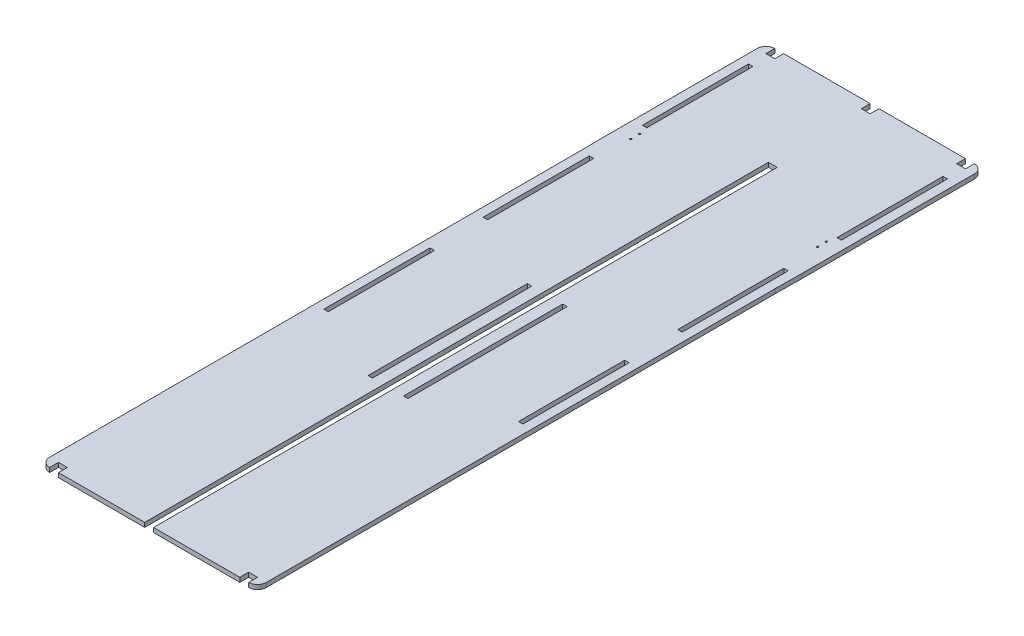
SolidWorks part; units mm, degrees
ref_plane "Front" through (0, 0, 0) normal (0, 0, 1) x (1, 0, 0)
ref_plane "Top" through (0, 0, 0) normal (0, 1, 0) x (1, 0, 0)
ref_plane "Right" through (0, 0, 0) normal (1, 0, 0) x (0, 0, -1)
sketch "Sketch2" plane through (0, 0, 0) normal (0, 1, 0) x (1, 0, 0)
  line L0 (122.5, 590) -> (122.5, -185) construction
  line L2 (0, 0) -> (0, 375)
  line L3 (0, 590) -> (245, 590)
  line L4 (245, -10) -> (245, 355)
  line L5 (10, 590) -> (10, -230) construction
  line L7 (117.5, -230) -> (117.5, 475)
  line L8 (117.5, 475) -> (127.5, 475)
  line L9 (127.5, -230) -> (127.5, 475)
  line L10 (117.5, -230) -> (127.5, 475) construction
  line L11 (117.5, 475) -> (127.5, -230) construction
  line L12 (10, -230) -> (15, -230)
  line L13 (15, -230) -> (15, 590) construction
  line L14 (235, 590) -> (235, -230) construction
  line L15 (235, -230) -> (230, -230)
  line L16 (230, -230) -> (230, 590) construction
  line L18 (0, 0) -> (0, -230)
  line L19 (245, -10) -> (245, -230)
  line L20 (0, -230) -> (117.5, -230)
  line L21 (127.5, -230) -> (245, -230)
  line L22 (-0.3, 405) -> (0, 375)
  line L23 (-0.3, 405) -> (-0.3, 590)
  line L24 (-0.3, 590) -> (0, 590)
  line L25 (10, 560) -> (15, 560)
  line L26 (245.3, 385) -> (245, 355)
  line L27 (245.3, 385) -> (245.3, 590)
  line L28 (245.3, 590) -> (245, 590)
  line L29 (10, 560) -> (10, 440)
  line L30 (10, 440) -> (15, 440)
  line L31 (15, 560) -> (15, 440)
  line L32 (15, 380) -> (10, 380)
  line L33 (15, 380) -> (15, 260)
  line L34 (15, 260) -> (10, 260)
  line L35 (10, 380) -> (10, 260)
  line L36 (10, 200) -> (15, 200)
  line L37 (10, 200) -> (10, 80)
  line L38 (10, 80) -> (15, 80)
  line L39 (15, 200) -> (15, 80)
  line L40 (230, 560) -> (235, 560)
  line L41 (230, 560) -> (230, 440)
  line L42 (230, 440) -> (235, 440)
  line L43 (235, 560) -> (235, 440)
  line L44 (230, 380) -> (235, 380)
  line L45 (230, 380) -> (230, 260)
  line L46 (230, 260) -> (235, 260)
  line L47 (235, 380) -> (235, 260)
  line L48 (230, 200) -> (235, 200)
  line L49 (230, 200) -> (230, 80)
  line L50 (230, 80) -> (235, 80)
  line L51 (235, 200) -> (235, 80)
  point P7 (122.5, 122.5)
  dimension "D1" = 245
  dimension "D2" = 820
  dimension "D3" = 115
  dimension "D4" = 10
  dimension "D5" = 590
  dimension "D6" = 10
  dimension "D7" = 5
  dimension "D8" = 10
  dimension "D9" = 5
  dimension "D10" = 30
  dimension "D11" = 120
  dimension "D12" = 60
  dimension "D13" = 0.3
  dimension "D14" = 30
  dimension "D15" = 30
  dimension "D16" = 120
  dimension "D17" = 60
  dimension "D18" = 120
  dimension "D19" = 120
  dimension "D20" = 60
  dimension "D21" = 120
  dimension "D22" = 60
  dimension "D23" = 120
extrude "Boss-Extrude1" add sketch "Sketch2" along normal blind 5
sketch "Sketch3" plane through (0, 5, 0) normal (0, 1, 0) x (1, 0, 0)
  line L0 (17, 510.3998) -> (17, 370) construction
  line L1 (0, -230) -> (0, 375) construction
  line L2 (-0.3, 590) -> (245.3, 590) construction
  line L3 (117.5, 475) -> (127.5, 475) construction
  line L4 (105, 220) -> (100, 220)
  line L5 (105, 220) -> (105, 40)
  line L6 (105, 40) -> (100, 40)
  line L7 (100, 220) -> (100, 40)
  line L8 (117.5, -230) -> (117.5, 475) construction
  circle A0 centre (17, 410) radius 1 construction
  circle A1 centre (17, 420) radius 1
  circle A2 centre (17, 430) radius 1
  circle A3 centre (17, 440) radius 1 construction
  dimension "D7" = 2
  dimension "D8" = 2
  dimension "D9" = 2
  dimension "D10" = 2
  dimension "D1" = 17
  dimension "D2" = 220
  dimension "D3" = 40
  dimension "D4" = 10
  dimension "D5" = 10
  dimension "D6" = 10
  dimension "D11" = 5
  dimension "D12" = 255
  dimension "D13" = 12.5
  dimension "D14" = 180
extrude "Cut-Extrude1" cut sketch "Sketch3" against normal blind 5
ref_plane "Plane1" through (122.5, 0, 0) normal (-1, 0, 0) x (0, 0, 1)
mirror "Mirror1" about plane through (122.5, 0, 0) normal (-1, 0, 0) of "Cut-Extrude1"
fillet "Fillet1" radius 10 4 edges at (245.3, 2.5, -590) (-0.3, 2.5, -590) (0, 2.5, 230) (245, 2.5, 230)
sketch "Sketch4" plane through (0, 5, 0) normal (0, 1, 0) x (1, 0, 0)
  line L0 (235.3, 590) -> (9.7, 590) construction
  line L1 (10, -230) -> (20, -230)
  line L2 (10, -230) -> (10, -220)
  line L3 (10, -220) -> (20, -220)
  line L4 (20, -230) -> (20, -220)
  line L5 (235, -230) -> (225, -230)
  line L6 (235, -230) -> (235, -220)
  line L7 (235, -220) -> (225, -220)
  line L8 (225, -230) -> (225, -220)
  line L9 (9.7, 590) -> (19.7, 590)
  line L10 (9.7, 590) -> (9.7, 580)
  line L11 (9.7, 580) -> (19.7, 580)
  line L12 (19.7, 590) -> (19.7, 580)
  line L13 (235.3, 590) -> (225.3, 590)
  line L14 (235.3, 590) -> (235.3, 580)
  line L15 (235.3, 580) -> (225.3, 580)
  line L16 (225.3, 590) -> (225.3, 580)
  line L17 (117.5, 590) -> (127.5, 590)
  line L18 (117.5, 590) -> (117.5, 580)
  line L19 (117.5, 580) -> (127.5, 580)
  line L20 (127.5, 590) -> (127.5, 580)
  point P26 (122.5, 590)
  point P27 (122.5, 590)
  dimension "D1" = 10
  dimension "D2" = 10
  dimension "D3" = 10
  dimension "D4" = 10
  dimension "D5" = 10
  dimension "D6" = 10
  dimension "D7" = 10
  dimension "D8" = 10
  dimension "D9" = 10
  dimension "D10" = 10
extrude "Cut-Extrude2" cut sketch "Sketch4" against normal blind 10
